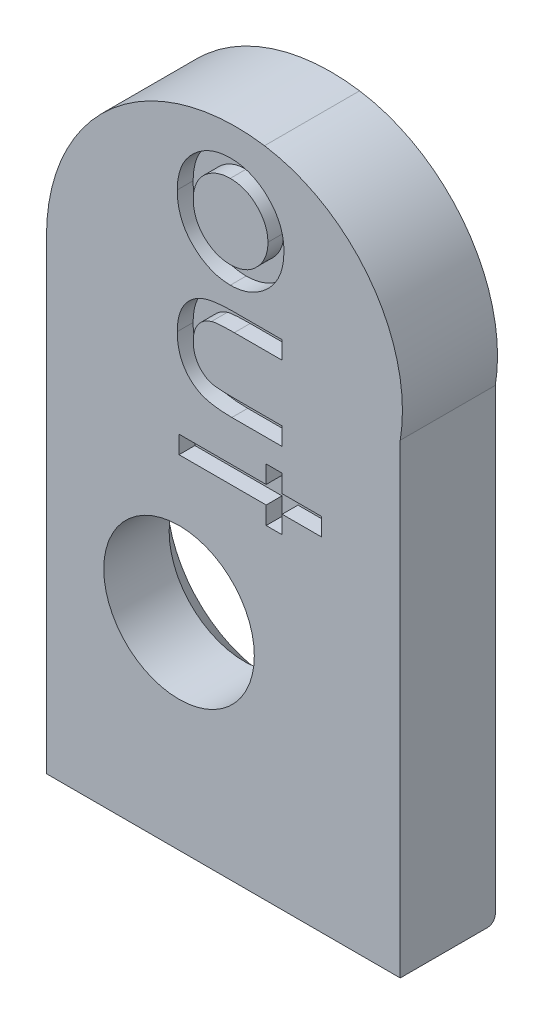
SolidWorks part; units mm, degrees
ref_plane "Front Plane" through (0, 0, 0) normal (0, 0, 1) x (1, 0, 0)
ref_plane "Top Plane" through (0, 0, 0) normal (0, 1, 0) x (1, 0, 0)
ref_plane "Right Plane" through (0, 0, 0) normal (1, 0, 0) x (0, 0, -1)
sketch "Sketch1" plane through (0, 0, 0) normal (0, 0, 1) x (1, 0, 0)
  line L0 (0, 0) -> (10.3566, 0) construction
  line L1 (0, 0) -> (6.5503, 11.3454) construction
  line L4 (-3.3457, 6.553) -> (-3.3457, -5.2)
  line L5 (-3.3457, -5.2) -> (5.5829, -5.2)
  line L6 (5.5829, 6.553) -> (5.5829, -5.2)
  arc A1 (-3.3457, 6.553) -> (2.157, 11.2786) centre (1.4348, 6.553) cw
  arc A2 (2.157, 11.2786) -> (5.5829, 6.553) centre (1.5375, 7.2249) cw
  dimension "D2" = 5.2
  dimension "D1" = 60
extrude "Boss-Extrude1" add sketch "Sketch1" along normal blind 2.4
sketch "Sketch3" plane through (0, 0, 0) normal (0, 0, 1) x (1, 0, 0)
  circle A0 centre (0, 0) radius 1.9
extrude "Cut-Extrude3" cut sketch "Sketch3" along normal through all
chamfer "Chamfer1" distance 0.75 angle 47 1 edges at (1.9, 0, 0)
fillet "Fillet1" radius 0.2 1 edges at (1.1186, -5.2, 0)
ref_plane "Plane1" through (0, 0, 2.4) normal (0, 0, 1) x (1, 0, 0)
sketch "Sketch4" plane through (0, 0, 2.4) normal (0, 0, 1) x (1, 0, 0)
  line L0 (0, 10.8057) -> (0, 2.2646) construction
  text T0 "<b>out</b>"
extrude "Cut-Extrude4" cut sketch "Sketch4" against normal blind 0.4
scale "Scale1" scale about centroid uniform scaling yes scale factor 1.15
